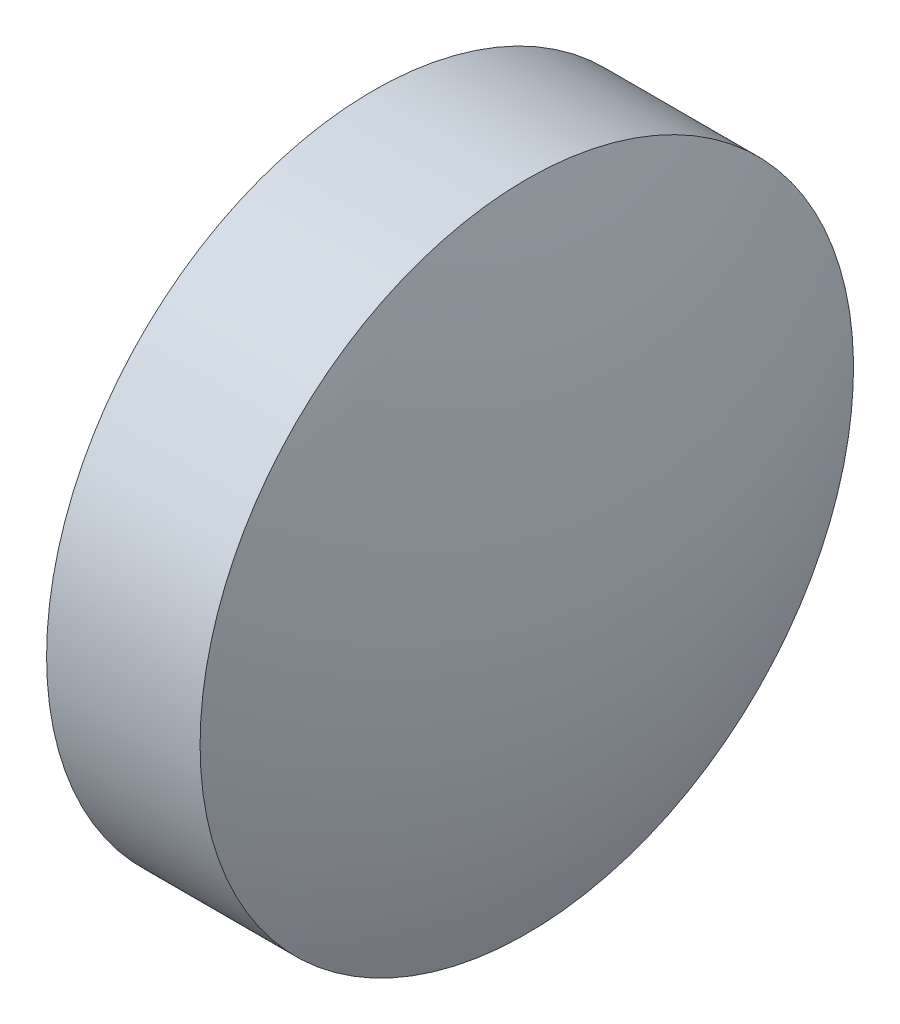
SolidWorks part; units mm, degrees
ref_plane "前视基准面" through (0, 0, 0) normal (0, 0, 1) x (1, 0, 0)
ref_plane "上视基准面" through (0, 0, 0) normal (0, 1, 0) x (1, 0, 0)
ref_plane "右视基准面" through (0, 0, 0) normal (1, 0, 0) x (0, 0, -1)
sketch "草图2" plane through (0, 0, 0) normal (0, 0, 1) x (1, 0, 0)
  line L0 (514.6266, 138.9246) -> (520.0049, 138.9246) construction
  line L1 (515.1163, 138.9246) -> (515.1163, 142.0746)
  line L2 (515.1163, 142.0746) -> (516.5963, 142.0746)
  line L3 (515.1163, 138.9246) -> (517.2163, 138.9246)
  arc A0 (517.2163, 138.9246) -> (516.5963, 142.0746) centre (508.9043, 138.9246) ccw
revolve "旋转2" add sketch "草图2" angle 360 about L0
